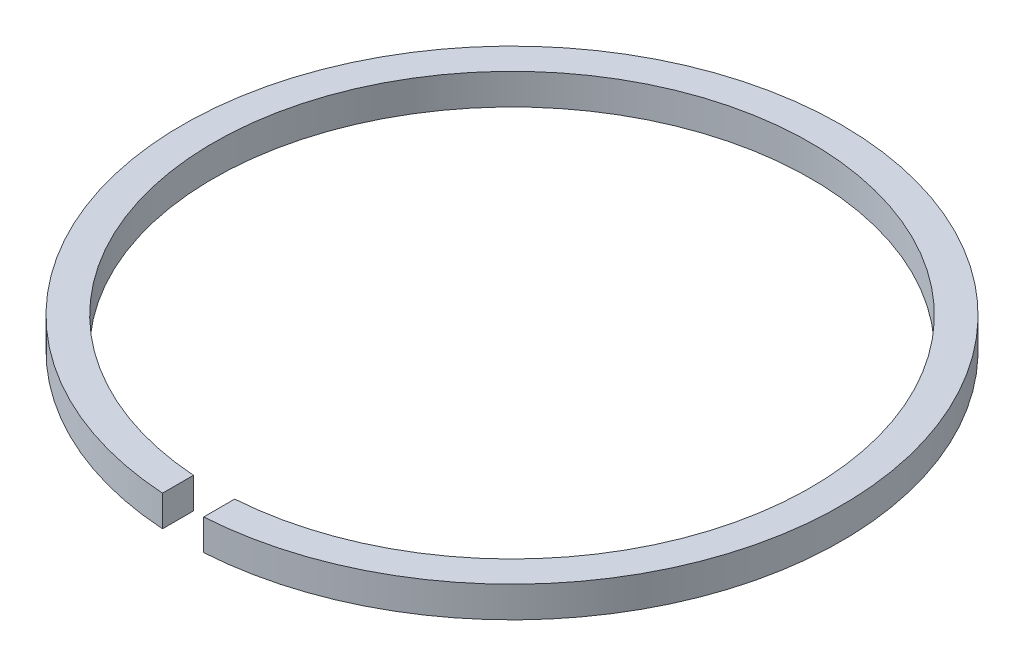
SolidWorks part; units mm, degrees
material "201 Annealed Stainless Steel (SS)"
ref_plane "Front Plane" through (0, 0, 0) normal (0, 0, 1) x (1, 0, 0)
ref_plane "Top Plane" through (0, 0, 0) normal (0, 1, 0) x (1, 0, 0)
ref_plane "Right Plane" through (0, 0, 0) normal (1, 0, 0) x (0, 0, -1)
sketch "Sketch1" plane through (0, 0, 0) normal (0, 1, 0) x (1, 0, 0)
  line L0 (0, 0) -> (0, -21.9731) construction
  line L1 (-1, -14.4655) -> (-1, -15.9687)
  line L2 (1, -14.4655) -> (1, -15.9687)
  arc A0 (1, -15.9687) -> (-1, -15.9687) centre (0, 0) ccw
  arc A1 (1, -14.4655) -> (-1, -14.4655) centre (0, 0) ccw
  dimension "D1" = 32
  dimension "D2" = 29
  dimension "D3" = 2
extrude "Body" add sketch "Sketch1" along normal mid plane 1.5
